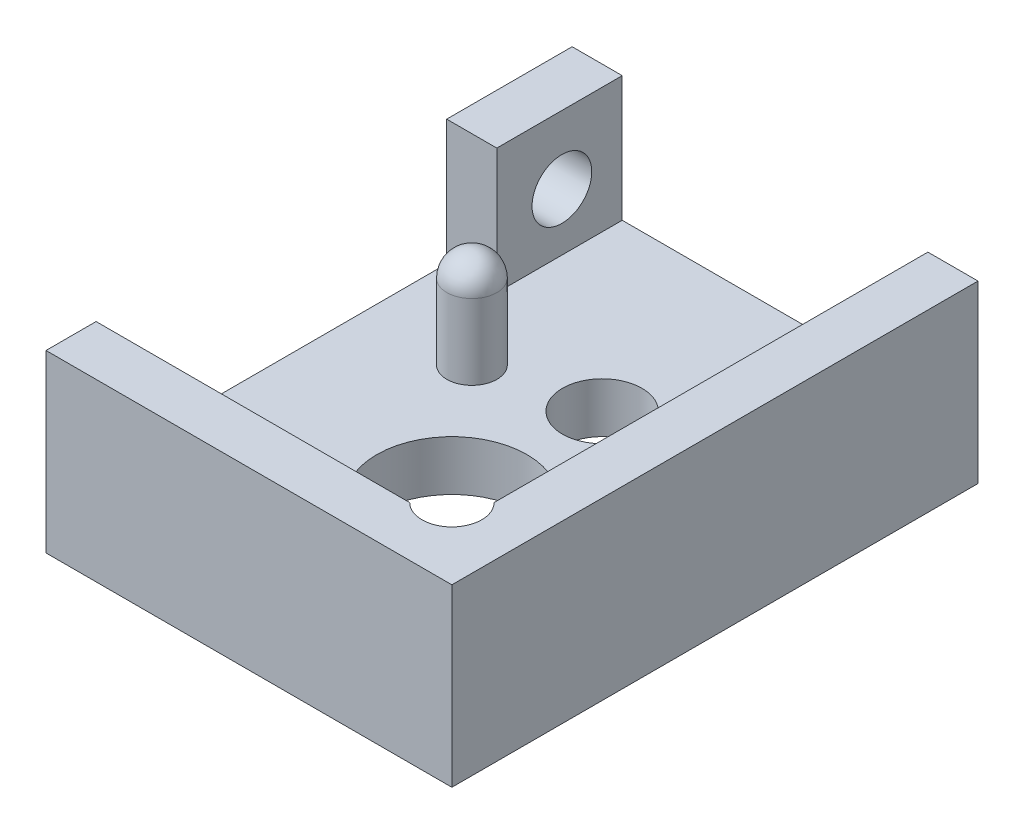
SolidWorks part; units mm, degrees
ref_plane "Front Plane" through (0, 0, 0) normal (0, 0, 1) x (1, 0, 0)
ref_plane "Top Plane" through (0, 0, 0) normal (0, 1, 0) x (1, 0, 0)
ref_plane "Right Plane" through (0, 0, 0) normal (1, 0, 0) x (0, 0, -1)
sketch "Sketch1" plane through (0, 0, 0) normal (0, 1, 0) x (1, 0, 0)
  line L7 (4.05, 5.75) -> (-4.05, 5.75)
  line L8 (4.05, 5.75) -> (4.05, -5.75)
  line L9 (4.05, -5.75) -> (-4.05, -5.75)
  line L10 (-4.05, 5.75) -> (-4.05, -5.75)
  line L11 (4.05, 5.75) -> (-4.05, -5.75) construction
  line L12 (4.05, -5.75) -> (-4.05, 5.75) construction
  point P0 (0, 0)
  point P6 (0, 0)
  dimension "D1" = 8.1
  dimension "D2" = 11.5
extrude "Boss-Extrude1" add sketch "Sketch1" along normal blind 3.5
sketch "Sketch2" plane through (0, 3.5, 0) normal (0, 1, 0) x (1, 0, 0)
  line L0 (-4.05, 5.75) -> (-4.05, -5.75) construction
  line L1 (3.05, 4.75) -> (-3.05, 4.75)
  line L2 (3.05, 4.75) -> (3.05, -4.75)
  line L3 (3.05, -4.75) -> (-3.05, -4.75)
  line L4 (-3.05, 4.75) -> (-3.05, -4.75)
  line L5 (3.05, 4.75) -> (-3.05, -4.75) construction
  line L6 (3.05, -4.75) -> (-3.05, 4.75) construction
  line L7 (4.05, 5.75) -> (-4.05, 5.75) construction
  point P0 (0, 0)
  dimension "D1" = 1
  dimension "D2" = 1
extrude "Cut-Extrude1" cut sketch "Sketch2" against normal offset from surface (2.5 mm away) 1 up to face at (0, 0, 0)
sketch "Sketch3" plane through (0, 1, 0) normal (0, 1, 0) x (1, 0, 0)
  line L0 (-3.05, -4.75) -> (3.05, -4.75) construction
  line L1 (3.05, -4.75) -> (3.05, 4.75) construction
  circle A0 centre (0.05, -1.75) radius 1.5
  dimension "D1" = 3
  dimension "D2" = 3
  dimension "D3" = 3
extrude "Cut-Extrude2" cut sketch "Sketch3" against normal through all
sketch "Sketch6" plane through (0, 3.5, 0) normal (0, 1, 0) x (1, 0, 0)
  line L0 (3.05, -4.75) -> (3.05, 4.75) construction
  line L2 (-3.05, -4.75) -> (3.05, -4.75) construction
  line L3 (3.05, -4.3291) -> (2.6291, -4.3291) construction
  line L4 (2.6291, -4.3291) -> (2.6291, -4.75) construction
  circle A3 centre (2.6291, -4.3291) radius 0.5953
  dimension "D1" = 1.1906
extrude "Cut-Extrude5" cut sketch "Sketch6" against normal up to surface (2.5 mm away) up to face at (0.05, 1, 3.25)
sketch "Sketch7" plane through (0, 1, 0) normal (0, 1, 0) x (1, 0, 0)
  line L0 (1.925, 1.25) -> (-1.825, 1.25) construction
  line L1 (-1.825, 1.25) -> (-1.825, -3.5) construction
  line L2 (-1.825, -3.5) -> (1.925, -3.5) construction
  line L3 (1.925, -3.5) -> (1.925, 1.25) construction
  line L4 (0.05, 1.25) -> (0.05, -1.75) construction
  circle A0 centre (0.05, 1.25) radius 0.7938
  circle A2 centre (-1.825, -3.5) radius 0.7938
  circle A3 centre (1.925, -3.5) radius 0.7938
  circle A4 centre (0.05, -1.75) radius 1.5 construction
  dimension "D1" = 1.5875
  dimension "D2" = 3.75
  dimension "D3" = 3
  dimension "D4" = 1.75
extrude "Cut-Extrude6" cut sketch "Sketch7" against normal through all
sketch "Sketch16" plane through (0, 0, 0) normal (0, -1, 0) x (1, 0, 0)
  line L0 (4.05, -5.75) -> (-4.05, -5.75) construction
  line L1 (4.2614, -4.75) -> (-4.7305, -4.75)
  line L2 (4.2614, -4.75) -> (4.2614, -5.75)
  line L3 (4.2614, -5.75) -> (-4.7305, -5.75)
  line L4 (-4.7305, -4.75) -> (-4.7305, -5.75)
  line L5 (3.05, -4.75) -> (-3.05, -4.75) construction
  line L8 (3.05, -4.75) -> (-3.05, -4.75) construction
extrude "Back-cut-extrude" cut sketch "Sketch16" against normal blind 4
sketch "Sketch17" plane through (0, 1, 0) normal (0, 1, 0) x (1, 0, 0)
  line L0 (-4.05, 4.75) -> (-4.05, -5.75) construction
  line L1 (-3.05, -4.75) -> (-4.05, -4.75)
  line L2 (-3.05, -4.75) -> (-3.05, 2.2465)
  line L3 (-3.05, 2.2465) -> (-4.05, 2.2465)
  line L4 (-4.05, -4.75) -> (-4.05, 2.2465)
  line L5 (-3.05, -4.75) -> (2.2081, -4.75) construction
extrude "Side-cut-extrude" cut sketch "Sketch17" along normal blind 3
sketch "Sketch18" plane through (0, 1, 0) normal (0, 1, 0) x (1, 0, 0)
  line L0 (-4.05, 2.2465) -> (-4.05, -4.75) construction
  line L2 (-4.05, -4.75) -> (2.2081, -4.75) construction
  circle A0 centre (-2.05, 0.75) radius 0.5
  dimension "D1" = 1
  dimension "D2" = 2
  dimension "D3" = 5.5
extrude "Peg-Extrude" add sketch "Sketch18" along normal blind 2
fillet "Fillet1" radius 0.5 1 edges at (-2.05, 3, -0.25)
hole_wizard "Tap Drill Slot for #0-80 Tap2" positions "Sketch23" profile "Sketch24" size "#0-80" standard "ANSI Inch" slot yes
sketch "Sketch23" plane through (-4.05, 0, 0) normal (-1, 0, 0) x (0, 0, 1)
  point P0 (-3.5458, 2.1437)
sketch "Sketch24" plane through (-4.05, 2.1437, -3.5458) normal (0, 1, 0) x (0, 0, 1)
  line L0 (0, 0) -> (0, 1.3579)
  line L1 (0, 1.3579) -> (0.5956, 1)
  line L2 (0.5956, 1) -> (0.5956, 0)
  line L5 (0.5956, 0) -> (0, 0)
  line L10 (0, 1.3579) -> (-0.5956, 1) construction
  line L11 (0, -6.35) -> (0, 107.95) construction
  dimension "Hole Dia." = 1.1913
  dimension "Hole Depth" = 1
  dimension "Drill Angle" = 118
